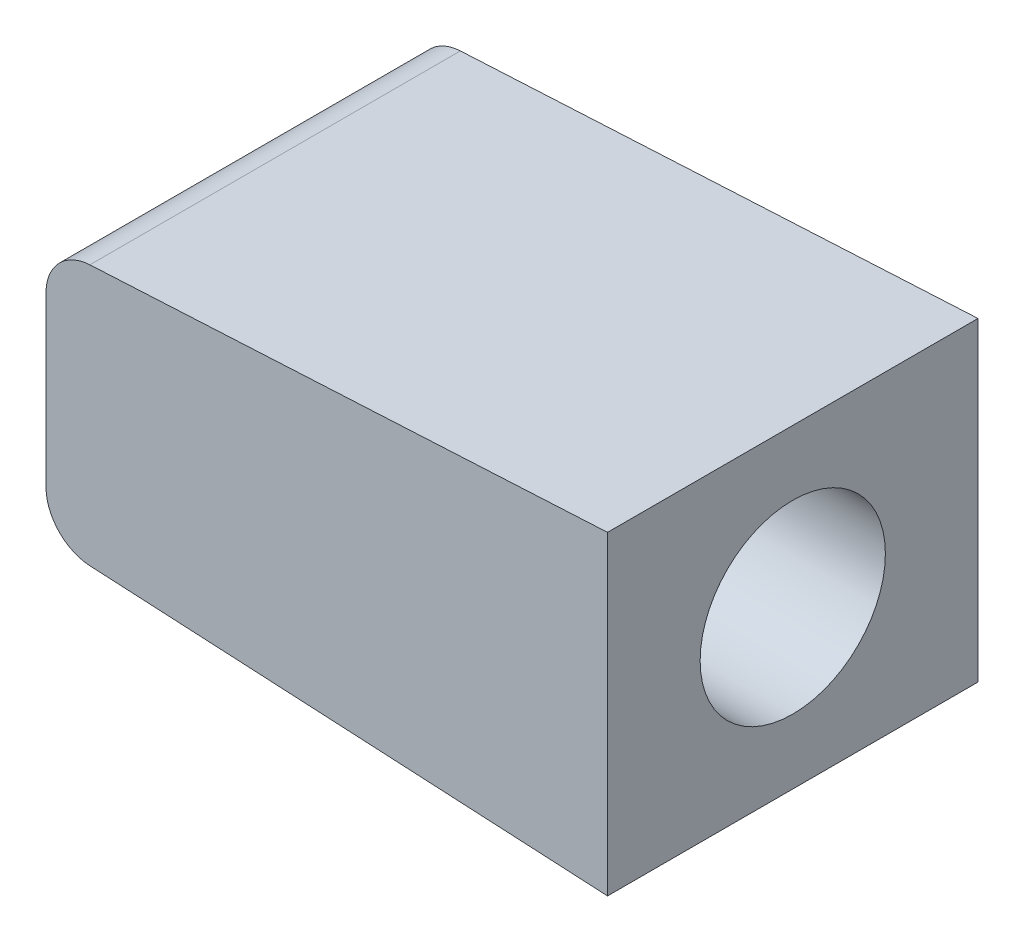
SolidWorks part; units mm, degrees
ref_plane "Front Plane" through (0, 0, 0) normal (0, 0, 1) x (1, 0, 0)
ref_plane "Top Plane" through (0, 0, 0) normal (0, 1, 0) x (1, 0, 0)
ref_plane "Right Plane" through (0, 0, 0) normal (1, 0, 0) x (0, 0, -1)
sketch "Esboço2" plane through (0, 0, 0) normal (0, 0, 1) x (1, 0, 0)
  line L0 (42.1251, 206.0437) -> (42.1251, 198.7184) construction
  line L1 (42.1251, 205.7811) -> (30.9477, 205.1953)
  line L4 (42.1251, 205.7811) -> (42.1251, 198.9811)
  line L5 (30, 204.1966) -> (30, 200.5655)
  line L6 (42.1251, 198.9811) -> (30.9477, 199.5669)
  line L7 (30, 206.0437) -> (30, 198.7184) construction
  arc A0 (30.9477, 199.5669) -> (30, 200.5655) centre (31, 200.5655) cw
  arc A1 (30.9477, 205.1953) -> (30, 204.1966) centre (31, 204.1966) ccw
  point P6 (42.1251, 202.3811)
  point P7 (42.1251, 202.3811)
  dimension "D2" = 1
  dimension "D1" = 6.8
extrude "Ressalto-extrusão1" add sketch "Esboço2" against normal up to vertex (8 mm away)
sketch "Esboço3" plane through (42.1251, 0, 0) normal (1, 0, 0) x (0, 0, -1)
  line L0 (4, 205.7811) -> (4, 198.9811) construction
  line L1 (8, 205.7811) -> (0, 205.7811) construction
  line L2 (8, 198.9811) -> (0, 198.9811) construction
  circle A0 centre (4, 202.3811) radius 2
  dimension "D1" = 4
extrude "Corte-extrusão1" cut sketch "Esboço3" against normal through all
